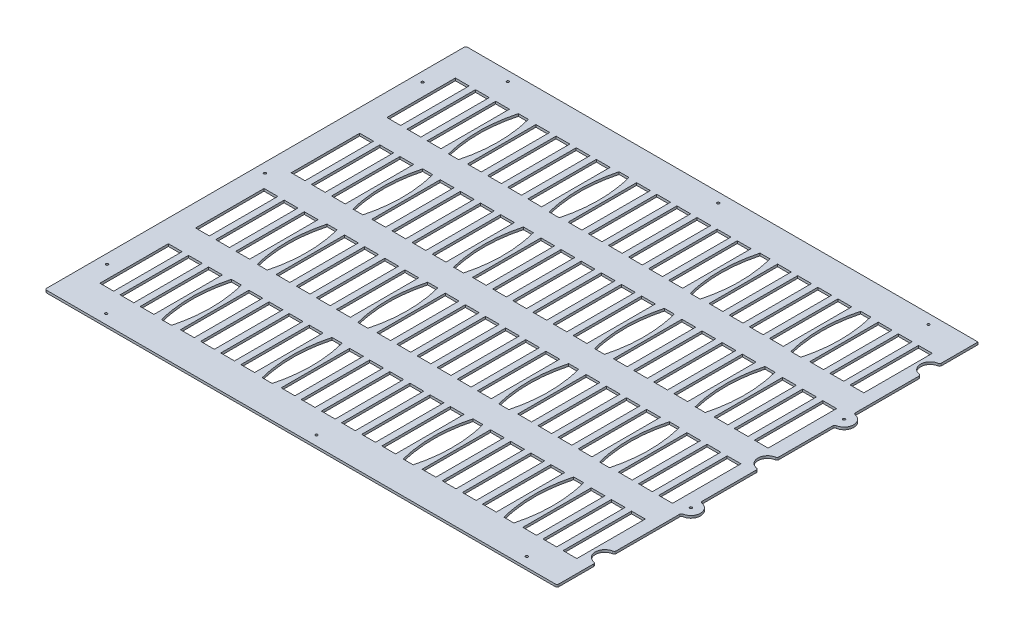
SolidWorks part; units mm, degrees
ref_plane "Front Plane" through (0, 0, 0) normal (0, 0, 1) x (1, 0, 0)
ref_plane "Top Plane" through (0, 0, 0) normal (0, 1, 0) x (1, 0, 0)
ref_plane "Right Plane" through (0, 0, 0) normal (1, 0, 0) x (0, 0, -1)
sketch "Sketch1" plane through (0, 0, 0) normal (0, 1, 0) x (1, 0, 0)
  line L0 (-340.1822, 0) -> (340.1822, 0) construction
  line L1 (-340.1822, -279.5524) -> (340.1822, -279.5524)
  line L2 (-340.1822, -279.5524) -> (-340.1822, 279.5524)
  line L3 (-340.1822, 279.5524) -> (340.1822, 279.5524)
  line L4 (340.1822, -279.5524) -> (340.1822, -228.7524)
  line L5 (-340.1822, -279.5524) -> (340.1822, 279.5524) construction
  line L6 (-340.1822, 279.5524) -> (340.1822, -279.5524) construction
  line L7 (340.1822, -89.0524) -> (340.1822, -12.7)
  line L8 (340.1822, -203.3524) -> (340.1822, -114.4524)
  line L9 (340.1822, 12.7) -> (340.1822, 89.0524)
  line L10 (340.1822, 114.4524) -> (340.1822, 203.3524)
  line L11 (340.1822, 228.7524) -> (340.1822, 279.5524)
  arc A0 (340.1822, 12.7) -> (340.1822, -12.7) centre (340.1822, 0) ccw
  arc A1 (340.1822, -114.4524) -> (340.1822, -89.0524) centre (340.1822, -101.7524) ccw
  arc A2 (340.1822, 89.0524) -> (340.1822, 114.4524) centre (340.1822, 101.7524) ccw
  arc A3 (340.1822, -203.3524) -> (340.1822, -228.7524) centre (340.1822, -216.0524) ccw
  arc A4 (340.1822, 228.7524) -> (340.1822, 203.3524) centre (340.1822, 216.0524) ccw
  point P0 (0, 0)
  dimension "D3" = 63.5
  dimension "D4" = 12.7
  dimension "D5" = 63.5
  dimension "D6" = 177.8
  dimension "D7" = 177.8
  dimension "D1" = 559.1048
  dimension "D2" = 680.3644
extrude "Boss-Extrude1" add sketch "Sketch1" along normal blind 3.175
sketch "Sketch23" plane through (0, 3.175, 0) normal (0, 1, 0) x (1, 0, 0)
  line L1 (322.8848, -236.0422) -> (304.5968, -236.0422)
  line L2 (322.8848, -236.0422) -> (322.8848, -145.1102)
  line L3 (322.8848, -145.1102) -> (304.5968, -145.1102)
  line L4 (304.5968, -236.0422) -> (304.5968, -145.1102)
  line L5 (340.1822, -203.3524) -> (340.1822, -114.4524) construction
  line L6 (-340.1822, -279.5524) -> (340.1822, -279.5524) construction
  dimension "D1" = 90.932
  dimension "D2" = 18.288
  dimension "D3" = 17.2974
  dimension "D4" = 43.5102
extrude "Cut-Extrude7" cut sketch "Sketch23" against normal through all
pattern_linear "LPattern1" count 24 spacing 26.7473 along (-1, 0, 0) skipping (3, 0), (8, 0), (15, 0), (20, 0) of "Cut-Extrude7"
pattern_linear "LPattern2" count 4 spacing 127.0762 along (0, 0, -1) of "LPattern1", "Cut-Extrude7"
sketch "Sketch24" plane through (0, 3.175, 0) normal (0, 1, 0) x (1, 0, 0)
  line L0 (251.1022, -236.0422) -> (215.8955, -145.1102) construction
  line L1 (220.7989, -190.5762) -> (246.1989, -190.5762) construction
  line L2 (240.1029, -144.2212) -> (226.8949, -144.2212)
  line L3 (240.1029, -144.2212) -> (240.1029, -236.9312) construction
  line L4 (240.1029, -236.9312) -> (226.8949, -236.9312)
  line L5 (226.8949, -144.2212) -> (226.8949, -236.9312) construction
  line L6 (240.1029, -144.2212) -> (226.8949, -236.9312) construction
  line L7 (240.1029, -236.9312) -> (226.8949, -144.2212) construction
  line L8 (106.3663, -236.9312) -> (93.1583, -236.9312)
  line L9 (106.3663, -144.2212) -> (93.1583, -144.2212)
  spline S0 degree 2 poles (226.8949, -236.9312) (214.7029, -190.5762) (226.8949, -144.2212) knots 0 0 0 1 1 1
  spline S1 degree 2 poles (240.1029, -236.9312) (252.2949, -190.5762) (240.1029, -144.2212) knots 0 0 0 1 1 1
  spline S2 degree 2 poles (93.1583, -236.9312) (80.9663, -190.5762) (93.1583, -144.2212) knots 0 0 0 1 1 1
  spline S3 degree 2 poles (106.3663, -236.9312) (118.5583, -190.5762) (106.3663, -144.2212) knots 0 0 0 1 1 1
  point P4 (233.4989, -190.5762)
  point P12 (233.4989, -190.5762)
  dimension "D1" = 13.208
  dimension "D2" = 92.71
  dimension "D3" = 25.4
  dimension "D4" = 2
extrude "Cut-Extrude8" cut sketch "Sketch24" against normal through all
pattern_linear "LPattern3" count 2 spacing 320.9678 along (1, 0, 0) count 4 spacing 127.0762 along (0, 0, -1) of "Cut-Extrude8"
hole_wizard "#25 (0.1495) Diameter Hole1" positions "Sketch18" profile "Sketch19" hole size "#25" standard "ANSI Inch"
sketch "Sketch18" plane through (0, 3.175, 0) normal (0, 1, 0) x (1, 0, 0)
  line L19 (340.1822, -241.8842) -> (-340.1822, -241.8842) construction
  line L20 (340.1822, -279.5524) -> (340.1822, -228.7524) construction
  line L21 (-340.1822, 279.5524) -> (-340.1822, -279.5524) construction
  line L22 (340.1822, -139.2682) -> (-340.1822, -139.2682) construction
  line L23 (340.1822, -203.3524) -> (340.1822, -114.4524) construction
  line L24 (313.7408, -236.0422) -> (313.7408, -254.0762) construction
  line L25 (304.5968, -236.0422) -> (322.8848, -236.0422) construction
  line L30 (313.7408, -241.8842) -> (313.7408, -139.2682) construction
  line L32 (286.9902, -241.8842) -> (286.9902, -139.2682) construction
  line L33 (260.2396, -241.8842) -> (260.2396, -139.2682) construction
  line L34 (233.4889, -241.8842) -> (233.4889, -139.2682) construction
  line L35 (206.7383, -241.8842) -> (206.7383, -139.2682) construction
  line L36 (179.9877, -241.8842) -> (179.9877, -139.2682) construction
  line L37 (153.2371, -241.8842) -> (153.2371, -139.2682) construction
  line L38 (126.4865, -241.8842) -> (126.4865, -139.2682) construction
  line L39 (99.7359, -241.8842) -> (99.7359, -139.2682) construction
  line L40 (72.9852, -241.8842) -> (72.9852, -139.2682) construction
  line L41 (46.2346, -241.8842) -> (46.2346, -139.2682) construction
  line L42 (19.484, -241.8842) -> (19.484, -139.2682) construction
  line L43 (-7.2666, -241.8842) -> (-7.2666, -139.2682) construction
  line L44 (-34.0172, -241.8842) -> (-34.0172, -139.2682) construction
  line L45 (-60.7678, -241.8842) -> (-60.7678, -139.2682) construction
  line L46 (-87.5185, -241.8842) -> (-87.5185, -139.2682) construction
  line L47 (-114.2691, -241.8842) -> (-114.2691, -139.2682) construction
  line L48 (-141.0197, -241.8842) -> (-141.0197, -139.2682) construction
  line L49 (-167.7703, -241.8842) -> (-167.7703, -139.2682) construction
  line L50 (-194.5209, -241.8842) -> (-194.5209, -139.2682) construction
  line L51 (-221.2715, -241.8842) -> (-221.2715, -139.2682) construction
  line L52 (-248.0222, -241.8842) -> (-248.0222, -139.2682) construction
  line L53 (-274.7728, -241.8842) -> (-274.7728, -139.2682) construction
  line L54 (-301.5234, -241.8842) -> (-301.5234, -139.2682) construction
  line L55 (251.1022, -236.0422) -> (269.3902, -236.0422) construction
  line L56 (322.8848, -145.1102) -> (304.5968, -145.1102) construction
  line L57 (-310.5914, -18.034) -> (-310.5914, -108.966) construction
  line L58 (-310.5914, -108.966) -> (-292.3034, -108.966) construction
  point P472 (313.7408, -139.2682)
  point P477 (286.9902, -139.2682)
  point P478 (260.2396, -241.8842)
  point P481 (233.4889, -139.2682)
  point P483 (206.7383, -139.2682)
  point P484 (179.9877, -241.8842)
  point P486 (153.2371, -241.8842)
  point P489 (126.4865, -139.2682)
  point P490 (99.7359, -241.8842)
  point P492 (72.9852, -241.8842)
  point P495 (46.2346, -139.2682)
  point P497 (19.484, -139.2682)
  point P498 (-7.2666, -241.8842)
  point P500 (-34.0172, -241.8842)
  point P503 (-60.7678, -139.2682)
  point P505 (-87.5185, -139.2682)
  point P506 (-114.2691, -241.8842)
  point P509 (-141.0197, -139.2682)
  point P511 (-167.7703, -139.2682)
  point P512 (-194.5209, -241.8842)
  point P514 (-221.2715, -241.8842)
  point P517 (-248.0222, -139.2682)
  point P518 (-274.7728, -241.8842)
  point P520 (-301.5234, -241.8842)
  point P575 (313.7408, -12.192)
  point P576 (286.9902, -12.192)
  point P577 (260.2396, -114.808)
  point P578 (233.4889, -12.192)
  point P579 (206.7383, -12.192)
  point P580 (179.9877, -114.808)
  point P581 (153.2371, -114.808)
  point P582 (126.4865, -12.192)
  point P583 (99.7359, -114.808)
  point P584 (72.9852, -114.808)
  point P585 (46.2346, -12.192)
  point P586 (19.484, -12.192)
  point P587 (-7.2666, -114.808)
  point P588 (-34.0172, -114.808)
  point P589 (-60.7678, -12.192)
  point P590 (-87.5185, -12.192)
  point P591 (-114.2691, -114.808)
  point P592 (-141.0197, -12.192)
  point P593 (-167.7703, -12.192)
  point P594 (-194.5209, -114.808)
  point P595 (-221.2715, -114.808)
  point P596 (-248.0222, -12.192)
  point P597 (-274.7728, -114.808)
  point P598 (-301.5234, -114.808)
  point P599 (313.7408, 114.8842)
  point P600 (286.9902, 114.8842)
  point P601 (260.2396, 12.2682)
  point P602 (233.4889, 114.8842)
  point P603 (206.7383, 114.8842)
  point P604 (179.9877, 12.2682)
  point P605 (153.2371, 12.2682)
  point P606 (126.4865, 114.8842)
  point P607 (99.7359, 12.2682)
  point P608 (72.9852, 12.2682)
  point P609 (46.2346, 114.8842)
  point P610 (19.484, 114.8842)
  point P611 (-7.2666, 12.2682)
  point P612 (-34.0172, 12.2682)
  point P613 (-60.7678, 114.8842)
  point P614 (-87.5185, 114.8842)
  point P615 (-114.2691, 12.2682)
  point P616 (-141.0197, 114.8842)
  point P617 (-167.7703, 114.8842)
  point P618 (-194.5209, 12.2682)
  point P619 (-221.2715, 12.2682)
  point P620 (-248.0222, 114.8842)
  point P621 (-274.7728, 12.2682)
  point P622 (-301.5234, 12.2682)
  point P623 (313.7408, 241.9604)
  point P624 (286.9902, 241.9604)
  point P625 (260.2396, 139.3444)
  point P626 (233.4889, 241.9604)
  point P627 (206.7383, 241.9604)
  point P628 (179.9877, 139.3444)
  point P629 (153.2371, 139.3444)
  point P630 (126.4865, 241.9604)
  point P631 (99.7359, 139.3444)
  point P632 (72.9852, 139.3444)
  point P633 (46.2346, 241.9604)
  point P634 (19.484, 241.9604)
  point P635 (-7.2666, 139.3444)
  point P636 (-34.0172, 139.3444)
  point P637 (-60.7678, 241.9604)
  point P638 (-87.5185, 241.9604)
  point P639 (-114.2691, 139.3444)
  point P640 (-141.0197, 241.9604)
  point P641 (-167.7703, 241.9604)
  point P642 (-194.5209, 139.3444)
  point P643 (-221.2715, 139.3444)
  point P644 (-248.0222, 241.9604)
  point P645 (-274.7728, 139.3444)
  point P646 (-301.5234, 139.3444)
  dimension "D1" = 5.842
  dimension "D2" = 5.842
  dimension "D5" = 9.068
  dimension "D6" = 96.774
  dimension "D3" = 24
  dimension "D4" = 4
sketch "Sketch19" plane through (-301.5234, 3.175, -139.3444) normal (1, 0, 0) x (0, 0, 1)
  line L0 (0, 0) -> (0, 3.175)
  line L1 (0, 3.175) -> (1.8986, 3.175)
  line L2 (1.8986, 3.175) -> (1.8986, 0)
  line L5 (1.8986, 0) -> (0, 0)
  line L11 (0, -6.35) -> (0, 107.95) construction
  dimension "Thru Hole Dia." = 3.7973
  dimension "Thru Hole Depth" = 3.175
fillet "Fillet1" radius 2.54 13 edges at (-340.1822, 1.5875, -279.5524) (-340.1822, 1.5875, 279.5524) (340.1822, 1.5875, 279.5524) (340.1822, 1.5875, 203.3524) (340.1822, 1.5875, 228.7524) (340.1822, 1.5875, -228.7524) (340.1822, 1.5875, -203.3524) (340.1822, 1.5875, -114.4524) (340.1822, 1.5875, -89.0524) (340.1822, 1.5875, -12.7) (340.1822, 1.5875, 12.7) (340.1822, 1.5875, 89.0524) (340.1822, 1.5875, 114.4524)
hole_wizard "#6 Clearance Hole1" positions "Sketch8" profile "Sketch9" hole size "#6" standard "ANSI Inch"
sketch "Sketch8" plane through (0, 3.175, 0) normal (0, 1, 0) x (1, 0, 0)
  line L13 (-292.227, 236.1184) -> (-283.771, 145.1864) construction
  line L15 (1.9569, 236.1184) -> (10.4129, 145.1864) construction
  line L17 (296.1408, 236.1184) -> (304.5968, 145.1864) construction
  line L18 (-292.227, 109.0422) -> (-283.771, 18.1102) construction
  line L19 (1.9569, 109.0422) -> (10.4129, 18.1102) construction
  line L20 (296.1408, 109.0422) -> (304.5968, 18.1102) construction
  line L21 (-292.227, -18.034) -> (-283.771, -108.966) construction
  line L22 (1.9569, -18.034) -> (10.4129, -108.966) construction
  line L23 (296.1408, -18.034) -> (304.5968, -108.966) construction
  line L24 (-292.227, -145.1102) -> (-283.771, -236.0422) construction
  line L25 (1.9569, -145.1102) -> (10.4129, -236.0422) construction
  line L26 (296.1408, -145.1102) -> (304.5968, -236.0422) construction
  point P129 (-287.999, 190.6524)
  point P131 (6.1849, 190.6524)
  point P133 (300.3688, 190.6524)
  point P146 (-287.999, 63.5762)
  point P147 (6.1849, 63.5762)
  point P148 (300.3688, 63.5762)
  point P155 (-287.999, -63.5)
  point P156 (6.1849, -63.5)
  point P157 (300.3688, -63.5)
  point P164 (-287.999, -190.5762)
  point P165 (6.1849, -190.5762)
  point P166 (300.3688, -190.5762)
  dimension "D1" = 4
sketch "Sketch9" plane through (300.3688, 3.175, 190.5762) normal (1, 0, 0) x (0, 0, 1)
  line L0 (0, 0) -> (0, 3.175)
  line L1 (0, 3.175) -> (1.8986, 3.175)
  line L2 (1.8986, 3.175) -> (1.8986, 0)
  line L5 (1.8986, 0) -> (0, 0)
  line L11 (0, -6.35) -> (0, 107.95) construction
  dimension "Thru Hole Dia." = 3.7973
  dimension "Thru Hole Depth" = 3.175
hole_wizard "#2 Clearance Hole1" positions "Sketch13" profile "Sketch14" hole size "#2" standard "ANSI Inch"
sketch "Sketch13" plane through (0, 3.175, 0) normal (0, 1, 0) x (1, 0, 0)
  line L9 (322.8848, -108.966) -> (322.8848, -18.034) construction
  line L10 (322.8848, -18.034) -> (304.5968, -18.034) construction
  line L18 (10.4129, 18.1102) -> (28.7009, -18.034) construction
  line L21 (5.6261, -13.9319) -> (33.5661, -13.9319) construction
  line L22 (5.6261, -13.9319) -> (5.6261, 14.0081) construction
  line L23 (5.6261, 14.0081) -> (33.5661, 14.0081) construction
  line L24 (33.5661, -13.9319) -> (33.5661, 14.0081) construction
  line L25 (5.6261, -13.9319) -> (33.5661, 14.0081) construction
  line L26 (5.6261, 14.0081) -> (33.5661, -13.9319) construction
  line L27 (10.4129, 18.1102) -> (28.7009, 18.1102) construction
  point P129 (5.6261, 14.0081)
  point P132 (5.6261, -13.9319)
  point P135 (33.5661, -13.9319)
  point P138 (33.5661, 14.0081)
  dimension "D1" = 27.94
  dimension "D2" = 27.94
  dimension "D3" = 4.1021
sketch "Sketch14" plane through (33.5661, 3.175, -14.0081) normal (1, 0, 0) x (0, 0, 1)
  line L0 (0, 0) -> (0, 3.175)
  line L1 (0, 3.175) -> (1.2192, 3.175)
  line L2 (1.2192, 3.175) -> (1.2192, 0)
  line L5 (1.2192, 0) -> (0, 0)
  line L11 (0, -6.35) -> (0, 107.95) construction
  dimension "Thru Hole Dia." = 2.4384
  dimension "Thru Hole Depth" = 3.175
sketch "Sketch20" [suppressed] plane through (0, 3.175, 0) normal (0, 1, 0) x (1, 0, 0)
  line L0 (5.6261, 14.0081) -> (33.5661, -13.9319) construction
  circle A0 centre (19.5961, 0.0381) radius 7.62
  dimension "D1" = 15.24
extrude "Cut-Extrude6" [suppressed] cut sketch "Sketch20" against normal through all
hole_wizard "1/8 (0.125) Diameter Hole1" positions "Sketch21" profile "Sketch22" hole size "1/8" standard "ANSI Inch" end condition through all
sketch "Sketch21" plane through (0, 3.175, 0) normal (0, 1, 0) x (1, 0, 0)
  point P0 (287.274, -266.8524)
  point P12 (287.274, 266.8524)
  point P15 (7.874, 266.8524)
  point P18 (-271.526, 266.8524)
  point P21 (-327.5584, 209.55)
  point P24 (-327.5584, 0)
  point P27 (-327.5584, -209.55)
  point P30 (-271.526, -266.8524)
  point P33 (7.874, -266.8524)
  point P56 (340.1822, 101.7524)
  point P59 (340.1822, -101.7524)
sketch "Sketch22" plane through (287.274, 3.175, 266.8524) normal (1, 0, 0) x (0, 0, 1)
  line L0 (0, 0) -> (0, 3.175)
  line L1 (0, 3.175) -> (1.5875, 3.175)
  line L2 (1.5875, 3.175) -> (1.5875, 0)
  line L5 (1.5875, 0) -> (0, 0)
  line L11 (0, -6.35) -> (0, 107.95) construction
  dimension "Thru Hole Dia." = 3.175
  dimension "Thru Hole Depth" = 3.175
